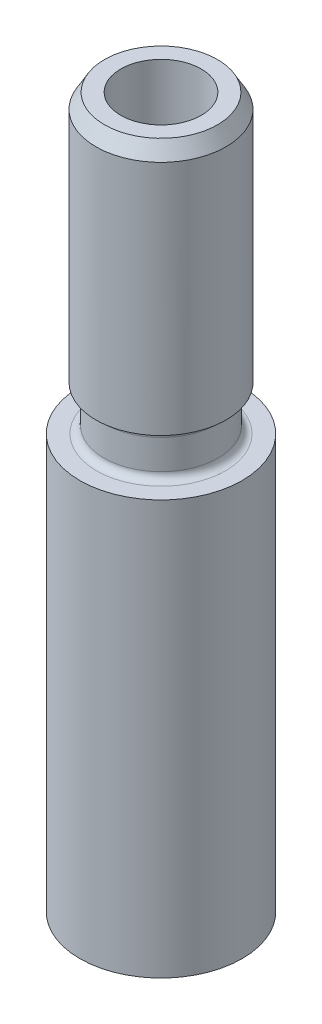
SolidWorks part; units mm, degrees
ref_plane "Front Plane" through (0, 0, 0) normal (0, 0, 1) x (1, 0, 0)
ref_plane "Top Plane" through (0, 0, 0) normal (0, 1, 0) x (1, 0, 0)
ref_plane "Right Plane" through (0, 0, 0) normal (1, 0, 0) x (0, 0, -1)
sketch "Sketch1" plane through (0, 0, 0) normal (0, 0, 1) x (1, 0, 0)
  line L0 (0, 0) -> (0, 38.1) construction
  line L1 (0, 0) -> (4.3561, 0)
  line L2 (4.3561, 0) -> (4.3561, 22.225)
  line L3 (4.3561, 22.225) -> (3.0607, 22.225)
  line L4 (3.0607, 22.225) -> (3.0607, 24.6063)
  line L5 (3.4925, 38.1) -> (2.159, 38.1)
  line L6 (2.159, 38.1) -> (2.159, 2.2732)
  line L7 (2.159, 2.2732) -> (0, 2.2732)
  line L8 (3.0607, 24.6063) -> (3.4925, 24.6063)
  line L9 (3.4925, 24.6063) -> (3.4925, 38.1)
  line L10 (0, 0) -> (0, 2.2732)
  dimension "D1" = 38.1
  dimension "D2" = 8.7122
  dimension "D3" = 6.1214
  dimension "D4" = 6.985
  dimension "D5" = 15.875
  dimension "D6" = 4.318
  dimension "D7" = 2.3813
revolve "Revolve1" add sketch "Sketch1" angle 360 about L0
chamfer "Chamfer1" distance 0.7937 angle 30 1 edges at (0, 38.1, -3.4925)
fillet "Fillet1" radius 0.3969 2 edges at (0, 24.6063, -3.0607) (0, 22.225, -3.0607)
